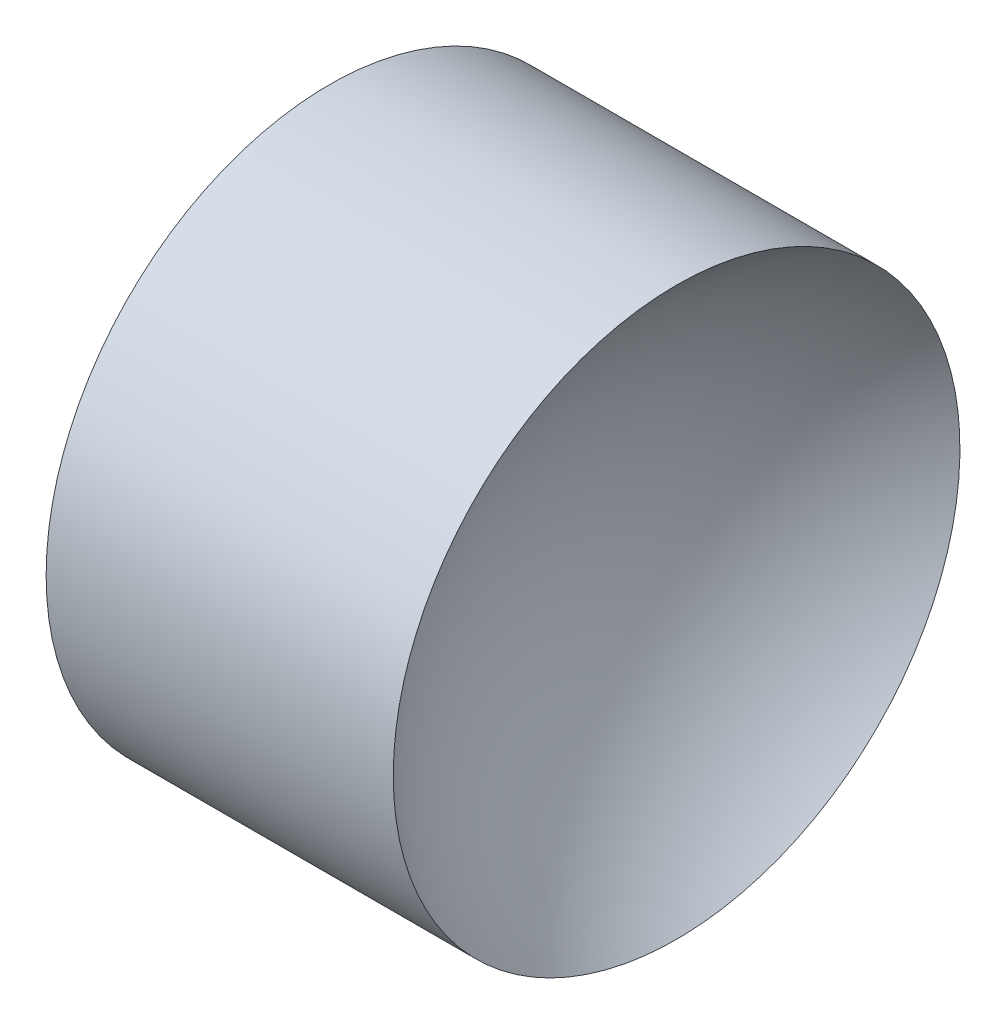
SolidWorks part; units mm, degrees
ref_plane "前视基准面" through (0, 0, 0) normal (0, 0, 1) x (1, 0, 0)
ref_plane "上视基准面" through (0, 0, 0) normal (0, 1, 0) x (1, 0, 0)
ref_plane "右视基准面" through (0, 0, 0) normal (1, 0, 0) x (0, 0, -1)
sketch "草图1" plane through (0, 0, 0) normal (0, 0, 1) x (1, 0, 0)
  line L0 (10.342, 6.5156) -> (13.4985, 6.5156) construction
  line L1 (11.157, 6.5156) -> (11.157, 8.5156)
  line L2 (12.657, 6.5156) -> (11.157, 6.5156)
  line L4 (11.157, 8.5156) -> (13.6071, 8.5156)
  arc A0 (13.6071, 8.5156) -> (12.657, 6.5156) centre (15.237, 6.5156) ccw
revolve "旋转1" add sketch "草图1" angle 360 about L0
